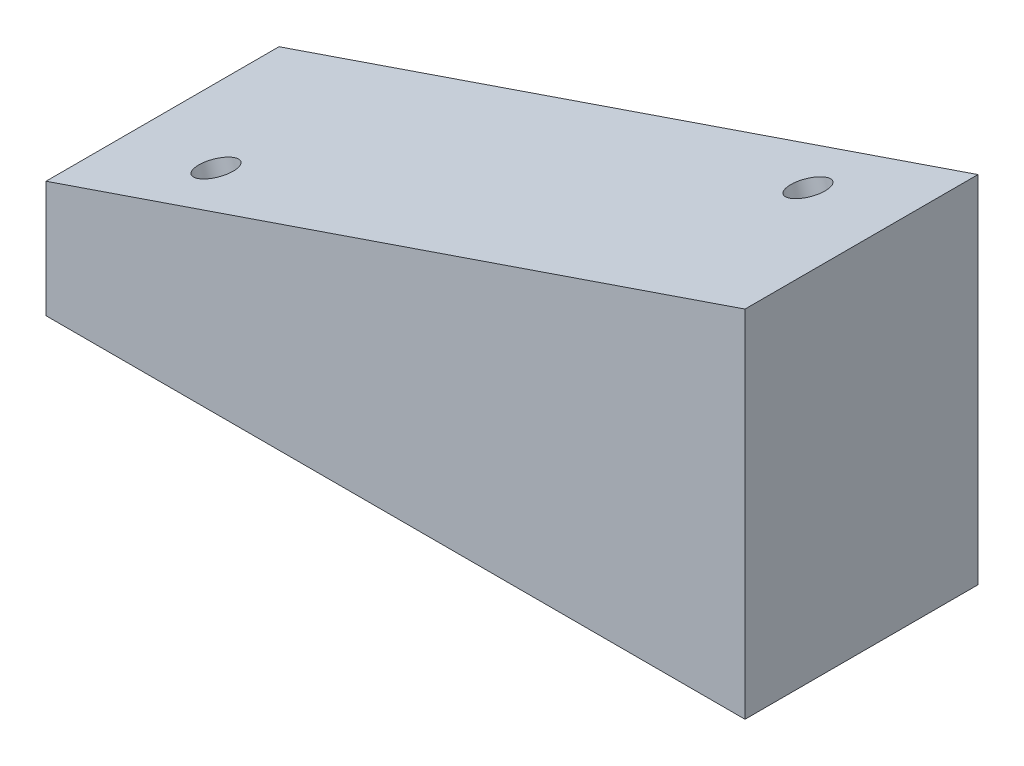
SolidWorks part; units mm, degrees
material "6061-T6 (SS)"
ref_plane "Front Plane" through (0, 0, 0) normal (0, 0, 1) x (1, 0, 0)
ref_plane "Top Plane" through (0, 0, 0) normal (0, 1, 0) x (1, 0, 0)
ref_plane "Right Plane" through (0, 0, 0) normal (1, 0, 0) x (0, 0, -1)
sketch "Sketch1" plane through (0, 0, 0) normal (0, 0, 1) x (1, 0, 0)
  line L0 (-76.2, 0) -> (76.2, 0)
  line L1 (76.2, 0) -> (76.2, 77.4593)
  line L2 (76.2, 77.4593) -> (-76.2, 25.4)
  line L3 (-76.2, 25.4) -> (-76.2, 0)
  point P3 (0, 0)
  dimension "D1" = 152.4
  dimension "D2" = 18.86
  dimension "D3" = 25.4
extrude "Boss-Extrude1" add sketch "Sketch1" against normal blind 50.8
hole_wizard "3/8-16 Tapped Hole1" positions "Sketch4" profile "Sketch3" tap size "3/8-16" standard "ANSI Inch"
sketch "Sketch4" plane through (-15.7324, 46.0555, 0) normal (-0.3233, 0.9463, 0) x (0.9463, 0.3233, 0)
  line L0 (-38.1438, 12.7) -> (71.3937, 38.1) construction
  line L2 (-63.8982, 50.8) -> (-63.8982, 0) construction
  line L3 (97.1482, 0) -> (-63.8982, 0) construction
  point P0 (-38.1438, 12.7)
  point P2 (71.3937, 38.1)
  point P10 (16.625, 25.4)
  point P14 (-63.8982, 25.4)
  point P22 (16.625, 0)
  dimension "D1" = 25.4
  dimension "D2" = 109.5375
cosmetic thread "Hole Thread1" parameters "D1"=19.05, "D2"=9.525
cosmetic thread "Hole Thread2" parameters "D1"=19.05, "D2"=9.525
sketch "Sketch3" plane through (-51.8283, 33.7253, -12.7) normal (0, 0, 1) x (-0.9463, -0.3233, 0)
  line L0 (0, 0) -> (0, 27.7847)
  line L1 (0, 27.7847) -> (3.9687, 25.4)
  line L2 (3.9687, 25.4) -> (3.9687, 0)
  line L5 (3.9687, 0) -> (0, 0)
  line L10 (0, 27.7847) -> (-3.9688, 25.4) construction
  line L11 (0, -6.35) -> (0, 107.95) construction
  dimension "Tap Drill Dia." = 7.9375
  dimension "Tap Drill Depth" = 25.4
  dimension "Drill Angle" = 118
hole_wizard "3/8-16 Tapped Hole2" positions "Sketch6" profile "Sketch5" tap size "3/8-16" standard "ANSI Inch"
sketch "Sketch6" plane through (0, 0, 0) normal (0, -1, 0) x (-1, 0, 0)
  line L0 (76.2, 50.8) -> (76.2, 0) construction
  line L1 (38.1, 25.4) -> (-38.1, 25.4) construction
  line L3 (76.2, 50.8) -> (-76.2, 50.8) construction
  point P0 (38.1, 25.4)
  point P2 (-38.1, 25.4)
  point P7 (76.2, 25.4)
  point P20 (0, 25.4)
  point P23 (0, 50.8)
  dimension "D1" = 76.2
cosmetic thread "Hole Thread3" parameters "D1"=19.05, "D2"=9.525
cosmetic thread "Hole Thread4" parameters "D1"=19.05, "D2"=9.525
sketch "Sketch5" plane through (-38.1, 0, -25.4) normal (1, 0, 0) x (0, 0, -1)
  line L0 (0, 0) -> (0, 27.7847)
  line L1 (0, 27.7847) -> (3.9687, 25.4)
  line L2 (3.9687, 25.4) -> (3.9687, 0)
  line L5 (3.9687, 0) -> (0, 0)
  line L10 (0, 27.7847) -> (-3.9688, 25.4) construction
  line L11 (0, -6.35) -> (0, 107.95) construction
  dimension "Tap Drill Dia." = 7.9375
  dimension "Tap Drill Depth" = 25.4
  dimension "Drill Angle" = 118
